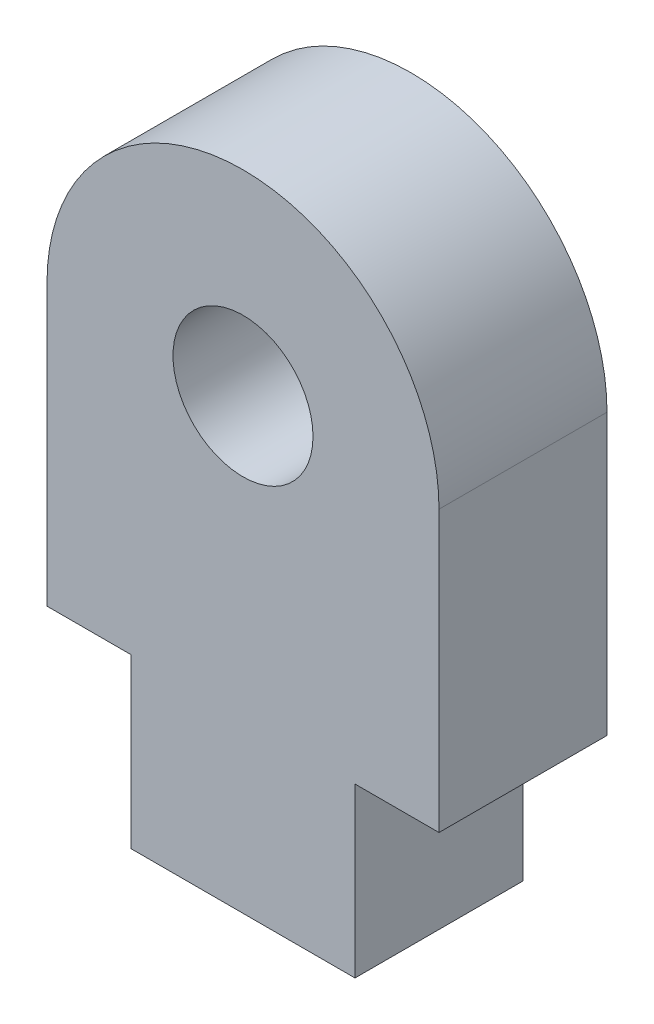
SolidWorks part; units mm, degrees
ref_plane "Front Plane" through (0, 0, 0) normal (0, 0, 1) x (1, 0, 0)
ref_plane "Top Plane" through (0, 0, 0) normal (0, 1, 0) x (1, 0, 0)
ref_plane "Right Plane" through (0, 0, 0) normal (1, 0, 0) x (0, 0, -1)
sketch "Sketch1" plane through (0, 0, 0) normal (0, 0, 1) x (1, 0, 0)
  line L0 (-3.5, 0) -> (-3.5, -5)
  line L1 (-3.5, -5) -> (-2, -5)
  line L2 (-2, -5) -> (-2, -8)
  line L3 (-2, -8) -> (2, -8)
  line L4 (2, -8) -> (2, -5)
  line L5 (2, -5) -> (3.5, -5)
  line L6 (3.5, -5) -> (3.5, 0)
  arc A0 (3.5, 0) -> (-3.5, 0) centre (0, 0) ccw
  circle A1 centre (0, 0) radius 1.25
  dimension "D1" = 2.5
  dimension "10" = 7
  dimension "D2" = 0
  dimension "D3" = 4
  dimension "D4" = 5
  dimension "D5" = 1.5
  dimension "D6" = 3
extrude "Boss-Extrude1" add sketch "Sketch1" along normal blind 3
